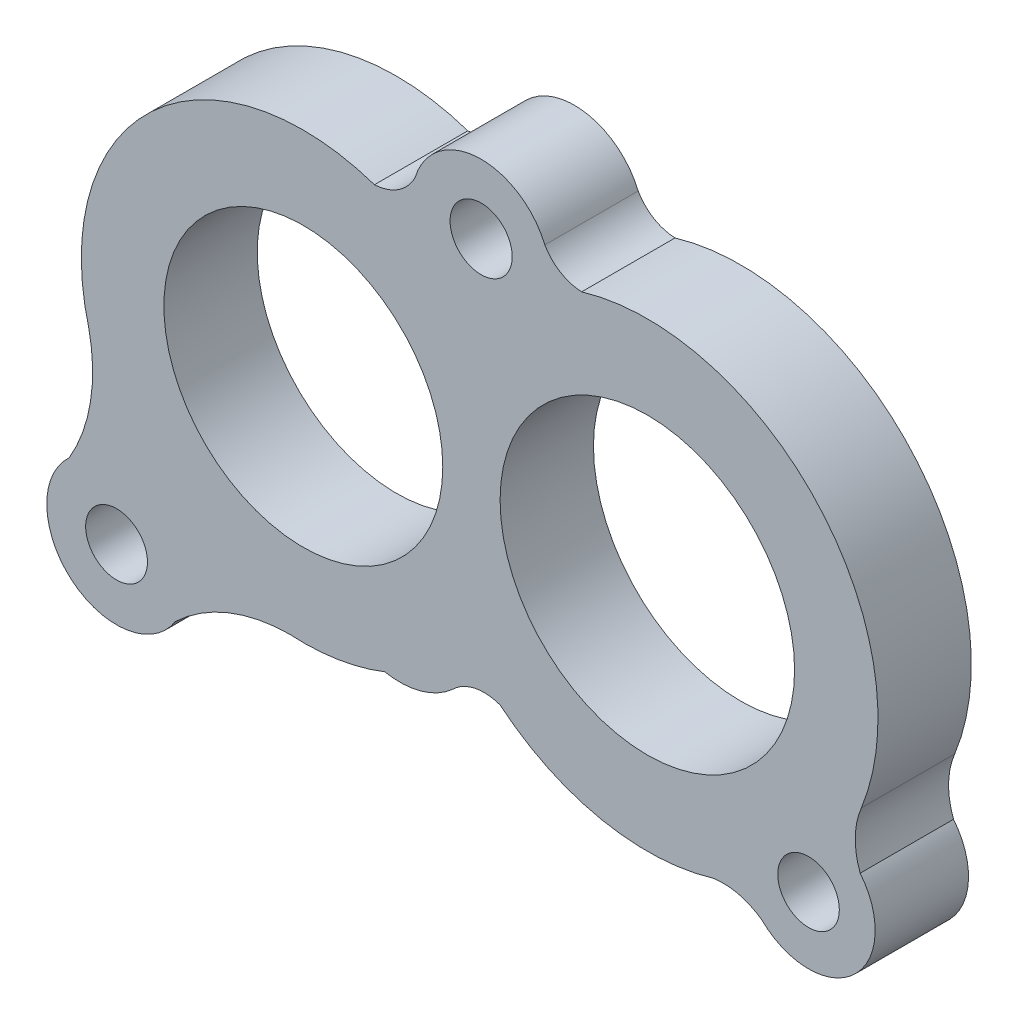
SolidWorks part; units mm, degrees
ref_plane "Front Plane" through (0, 0, 0) normal (0, 0, 1) x (1, 0, 0)
ref_plane "Top Plane" through (0, 0, 0) normal (0, 1, 0) x (1, 0, 0)
ref_plane "Right Plane" through (0, 0, 0) normal (1, 0, 0) x (0, 0, -1)
sketch "Sketch2" plane through (0, 0, 0) normal (0, 0, 1) x (1, 0, 0)
  line L0 (1172.8971, 712.9126) -> (1204.3971, 712.9126) construction
  circle A0 centre (1188.539, 712.6369) radius 15.7751
  circle A1 centre (1151.6841, 712.6369) radius 14.9392
  arc A4 (1172.7639, 693.6189) -> (1195.6301, 688.9672) centre (1188.539, 712.6369) ccw
  circle A5 centre (1131.6749, 687.9851) radius 3.3107
  circle A6 centre (1170.7329, 735.8529) radius 3.329
  arc A8 (1177.559, 738.701) -> (1181.5067, 736.324) centre (1181.6596, 741.0447) ccw
  arc A9 (1159.3039, 735.1579) -> (1163.6436, 737.9622) centre (1159.0553, 740.3027) ccw
  arc A12 (1177.559, 738.701) -> (1163.6436, 737.9622) centre (1170.7329, 735.8529) ccw
  arc A13 (1126.5981, 693.4726) -> (1137.9863, 683.9784) centre (1131.6749, 687.9851) ccw
  arc A14 (1137.9863, 683.9784) -> (1150.1916, 688.9086) centre (1150.3251, 671.0051) cw
  arc A15 (1126.5981, 693.4726) -> (1128.71, 706.5172) centre (1110.929, 702.7027) ccw
  arc A16 (1167.6753, 692.5312) -> (1172.7639, 693.6189) centre (1171.0712, 689.0912) cw
  arc A17 (1160.4053, 690.519) -> (1167.6753, 692.5312) centre (1162.0249, 698.8064) ccw
  circle A18 centre (1205.8073, 692.7915) radius 3.2967
  arc A19 (1200.8191, 687.6835) -> (1211.3405, 697.3035) centre (1205.8073, 692.7915) ccw
  arc A20 (1211.4674, 703.4269) -> (1211.3405, 697.3035) centre (1219.0137, 700.2075) ccw
  arc A21 (1195.6301, 688.9672) -> (1200.8191, 687.6835) centre (1196.6641, 682.0177) cw
  arc A22 (1159.3039, 735.1579) -> (1128.71, 706.5172) centre (1151.6576, 712.6652) ccw
  arc A23 (1211.3684, 703.1841) -> (1181.5067, 736.324) centre (1188.539, 712.6369) ccw
  arc A24 (1150.1916, 688.9086) -> (1160.4053, 690.519) centre (1151.6851, 712.6305) ccw
  dimension "D1" = 31.5
extrude "Boss-Extrude1" add sketch "Sketch2" along normal blind 10
